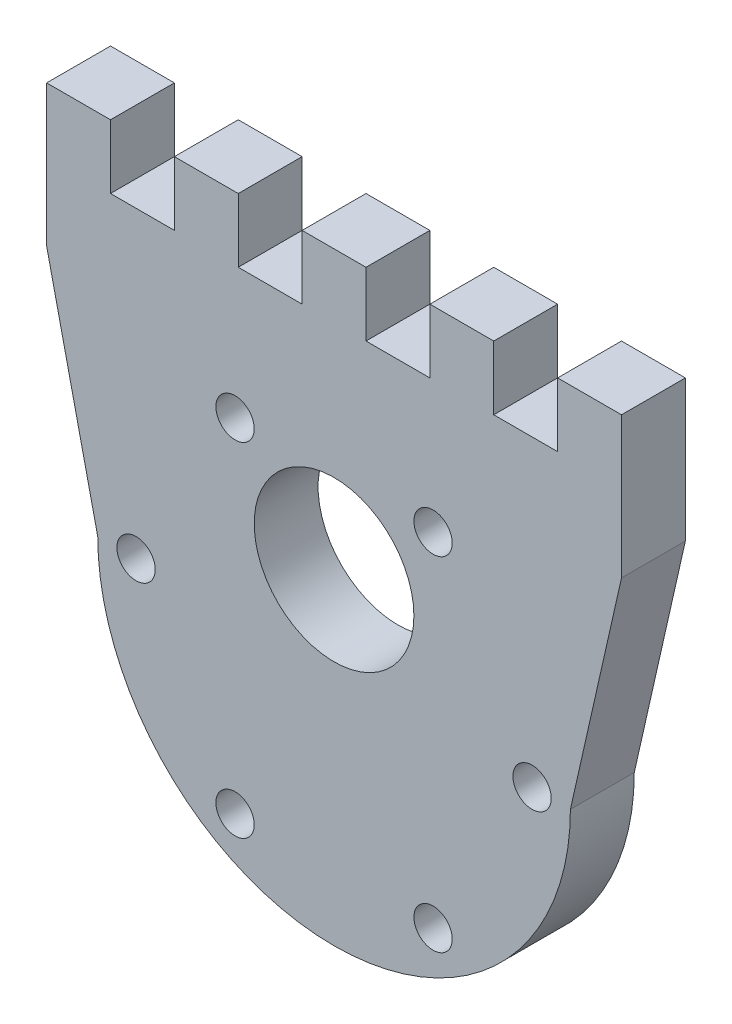
SolidWorks part; units mm, degrees
ref_plane "Plan de face" through (0, 0, 0) normal (0, 0, 1) x (1, 0, 0)
ref_plane "Plan de dessus" through (0, 0, 0) normal (0, 1, 0) x (1, 0, 0)
ref_plane "Plan de droite" through (0, 0, 0) normal (1, 0, 0) x (0, 0, -1)
sketch "Esquisse1" plane through (0, 0, 0) normal (0, 0, 1) x (1, 0, 0)
  line L0 (-25, 28.75) -> (25, 28.75)
  line L1 (25, 28.75) -> (18.5, 0)
  line L2 (-25, 28.75) -> (-18.5, 0)
  line L3 (0, -39.6591) -> (0, 82.1765) construction
  circle A0 centre (0, 0) radius 18.5 construction
  arc A1 (18.5, 0) -> (-18.5, 0) centre (0, 0) cw
  dimension "D1" = 37
  dimension "D2" = 50
  dimension "D3" = 25
  dimension "D4" = 28.75
extrude "Boss.-Extru.2" add sketch "Esquisse1" along normal blind 5 contours A1 L1 L0 L2
sketch "Esquisse2" plane through (0, 0, 5) normal (0, 0, 1) x (1, 0, 0)
  line L0 (0, 10.4176) -> (0, -31.7577) construction
  line L1 (-18.2103, -31.5411) -> (0, 0) construction
  circle A0 centre (-7.75, -13.4234) radius 1.5
  dimension "D2" = 3
  dimension "D1" = 15.5
  dimension "D3" = 0
  dimension "D4" = 30
extrude "Enlèv. mat.-Extru.1" cut sketch "Esquisse2" against normal blind 5
pattern_circular "Répétition circulaire1" count 6 over 360 about axis through (0, 0, 0) along (0, 0, 1) of "Enlèv. mat.-Extru.1"
sketch "Esquisse3" plane through (0, 0, 5) normal (0, 0, 1) x (1, 0, 0)
  circle A0 centre (0, 7) radius 6.25
  dimension "D2" = 12.5
  dimension "D1" = 7
extrude "Enlèv. mat.-Extru.2" cut sketch "Esquisse3" against normal blind 5 contours A0
sketch "Esquisse4" plane through (0, 0, 5) normal (0, 0, 1) x (1, 0, 0)
  line L0 (-25, 28.75) -> (25, 28.75) construction
  line L1 (-17.5, 28.75) -> (-12.5, 28.75)
  line L2 (-17.5, 28.75) -> (-17.5, 23.75)
  line L3 (-17.5, 23.75) -> (-12.5, 23.75)
  line L4 (-12.5, 28.75) -> (-12.5, 23.75)
  dimension "D1" = 7.5
  dimension "D2" = 5
  dimension "D3" = 5
extrude "Enlèv. mat.-Extru.3" cut sketch "Esquisse4" against normal blind 10
pattern_linear "Répétition linéaire1" count 4 spacing 10 along (1, 0, 0) of "Enlèv. mat.-Extru.3"
sketch "Esquisse5" plane through (0, 0, 5) normal (0, 0, 1) x (1, 0, 0)
  line L0 (-17.5, 28.75) -> (-17.5, 23.75) construction
  line L1 (22.5, 39.9194) -> (33.6569, 39.9194)
  line L2 (22.5, 39.9194) -> (22.5, 7.2456)
  line L3 (22.5, 7.2456) -> (33.6569, 7.2456)
  line L4 (33.6569, 39.9194) -> (33.6569, 7.2456)
  line L5 (-39.0933, 39.9194) -> (-22.5, 39.9194)
  line L6 (-39.0933, 39.9194) -> (-39.0933, 7.2456)
  line L7 (-39.0933, 7.2456) -> (-22.5, 7.2456)
  line L8 (-22.5, 39.9194) -> (-22.5, 7.2456)
  line L9 (17.5, 23.75) -> (17.5, 28.75) construction
  dimension "D1" = 5
  dimension "D2" = 5
extrude "Enlèv. mat.-Extru.4" cut sketch "Esquisse5" against normal blind 10
